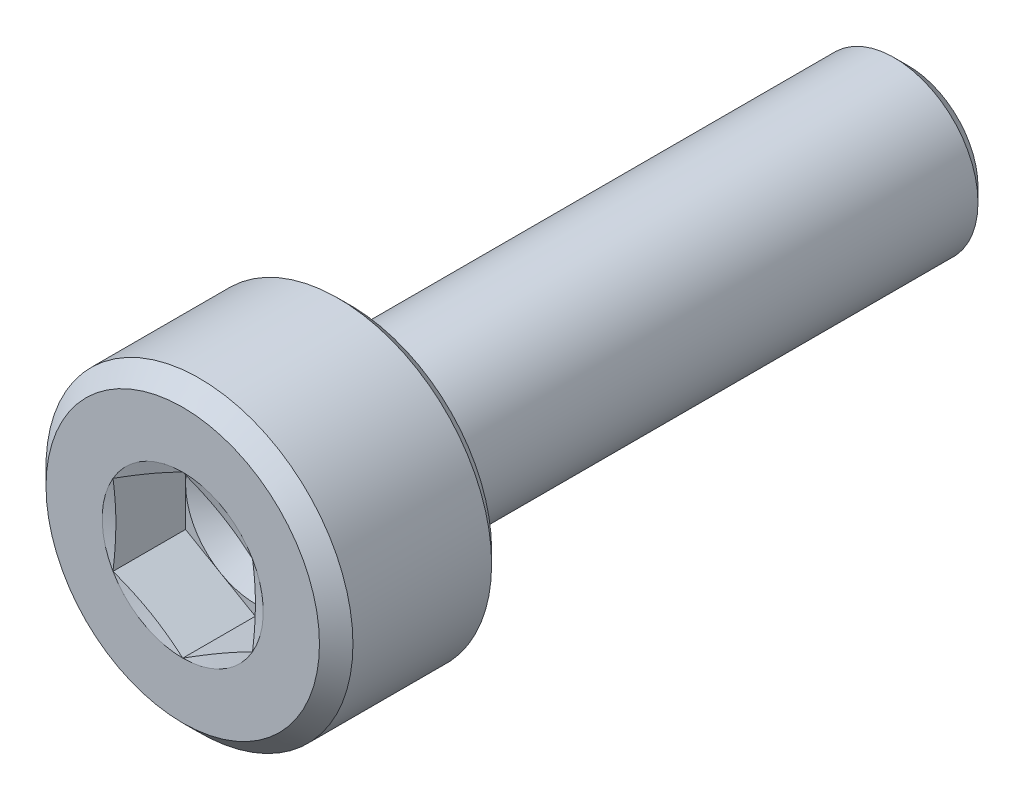
SolidWorks part; units mm, degrees
ref_plane "Front Plane" through (0, 0, 0) normal (0, 0, 1) x (1, 0, 0)
ref_plane "Top Plane" through (0, 0, 0) normal (0, 1, 0) x (1, 0, 0)
ref_plane "Right Plane" through (0, 0, 0) normal (1, 0, 0) x (0, 0, -1)
sketch "Sketch1" plane through (0, 0, 0) normal (1, 0, 0) x (0, 0, -1)
  line L0 (0, 0) -> (12.9407, 0) construction
  line L1 (0, 0) -> (0, 2.45)
  line L2 (0, 2.45) -> (0.3, 2.75)
  line L3 (0.3, 2.75) -> (2.785, 2.75)
  line L4 (3, 2.535) -> (3, 1.8)
  line L5 (3.51, 1.5) -> (12.75, 1.5)
  line L6 (12.75, 1.5) -> (13, 1.25)
  line L7 (13, 1.25) -> (13, 0)
  line L8 (13, 0) -> (0, 0)
  line L9 (2.785, 2.75) -> (3, 2.535)
  line L10 (3.4662, 1.5101) -> (3.0562, 1.7101)
  arc A2 (3.51, 1.5) -> (3.4662, 1.5101) centre (3.51, 1.6) cw
  arc A3 (3.0562, 1.7101) -> (3, 1.8) centre (3.1, 1.8) cw
  point P6 (3, 2.75)
  dimension "R2" = 0.1
  dimension "R1" = 0.1
  dimension "D1" = 45
  dimension "DK" = 5.5
  dimension "D3" = 45
  dimension "length" = 10
  dimension "K" = 3
  dimension "V" = 0.3
  dimension "HOLESIZE" = 3
  dimension "D4" = 2.5
  dimension "D5" = 45
  dimension "DW" = 5.07
  dimension "F" = 0.51
  dimension "DA" = 3.6
revolve "Revolve1" add sketch "Sketch1" angle 360 about L0
cosmetic thread "Cosmetic Thread1" parameters "D1"=8.5, "D2"=3
sketch "Sketch2" plane through (0, 0, 0) normal (0, 0, 1) x (1, 0, 0)
  line L0 (0, 0) -> (0, 1.4434) construction
  line L2 (0, 1.4434) -> (-1.25, 0.7217)
  line L3 (-1.25, 0.7217) -> (-1.25, -0.7217)
  line L4 (-1.25, -0.7217) -> (0, -1.4434)
  line L5 (0, -1.4434) -> (1.25, -0.7217)
  line L6 (1.25, -0.7217) -> (1.25, 0.7217)
  line L7 (1.25, 0.7217) -> (0, 1.4434)
  circle A0 centre (0, 0) radius 1.25 construction
  dimension "S" = 2.5
extrude "Cut-Extrude1" cut sketch "Sketch2" against normal blind 1.3
sketch "Sketch3" plane through (0, 0, 0) normal (1, 0, 0) x (0, 0, -1)
  line L0 (1.3, 0) -> (13, 0) construction
  line L1 (13, -1.25) -> (13, 1.25) construction
  line L2 (1.3, 0) -> (1.3, 1.25)
  line L4 (1.3, 1.25) -> (2.0217, 0)
  line L5 (2.0217, 0) -> (1.3, 0)
  line L6 (0, 2.45) -> (0, -2.45) construction
  dimension "DRILLANG" = 60
  dimension "DRILL DEPTH" = 1.3
  dimension "S2" = 2.5
revolve "Cut-Revolve2" cut sketch "Sketch3" angle 360 about L0
sketch "Sketch4" plane through (0, 0, 0) normal (1, 0, 0) x (0, 0, -1)
  line L0 (0, 0) -> (4.6121, 0) construction
  line L1 (0, 1.4434) -> (0, 1.25)
  line L2 (0, 2.45) -> (0, -2.45) construction
  line L3 (0, 1.25) -> (0.0518, 1.25)
  line L4 (0.0518, 1.25) -> (0, 1.4434)
  point P12 (0.0259, 1.25)
  dimension "D1" = 2.5
  dimension "D2" = 15
revolve "Cut-Revolve3" cut sketch "Sketch4" angle 360 about L0
